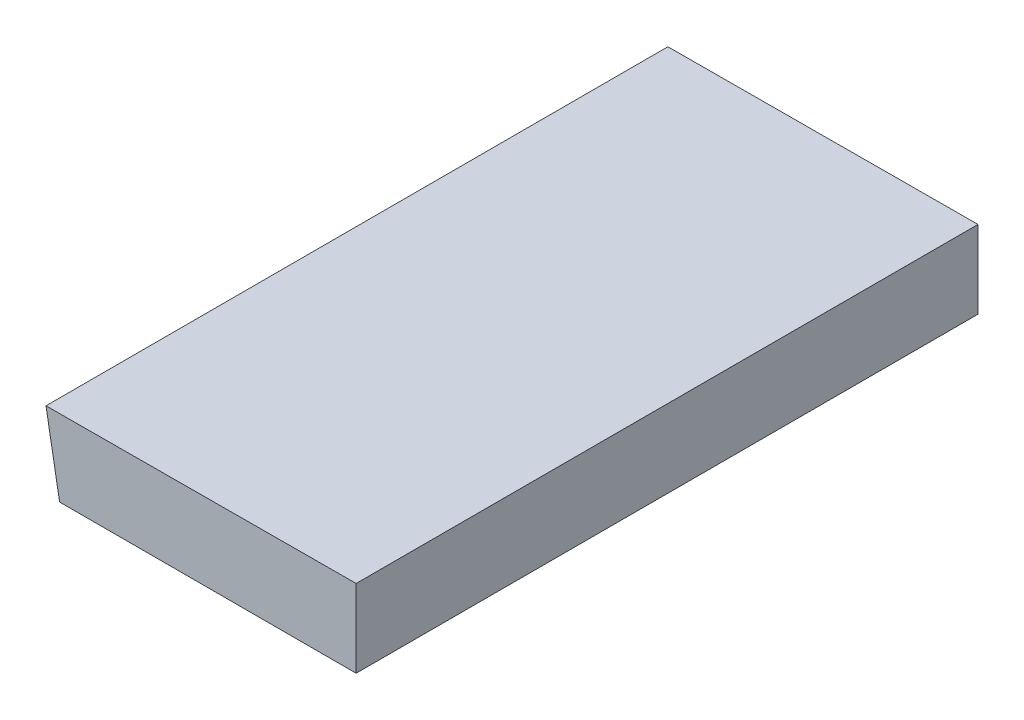
SolidWorks part; units mm, degrees
ref_plane "Front Plane" through (0, 0, 0) normal (0, 0, 1) x (1, 0, 0)
ref_plane "Top Plane" through (0, 0, 0) normal (0, 1, 0) x (1, 0, 0)
ref_plane "Right Plane" through (0, 0, 0) normal (1, 0, 0) x (0, 0, -1)
sketch "Sketch1" plane through (0, 0, 0) normal (0, 0, 1) x (1, 0, 0)
  line L6 (0, 0) -> (3.028, 0)
  line L11 (3.028, 0) -> (3.028, 0.794)
  line L12 (0, 0) -> (-0.1388, 0.7818)
  line L13 (-0.1388, 0.7818) -> (3.028, 0.794)
  dimension "D1" = 0.794
  dimension "D2" = 3.028
  dimension "D3" = 90
  dimension "D4" = 100.068
  dimension "D5" = 0.794
extrude "Boss-Extrude1" add sketch "Sketch1" along normal blind 6.35
